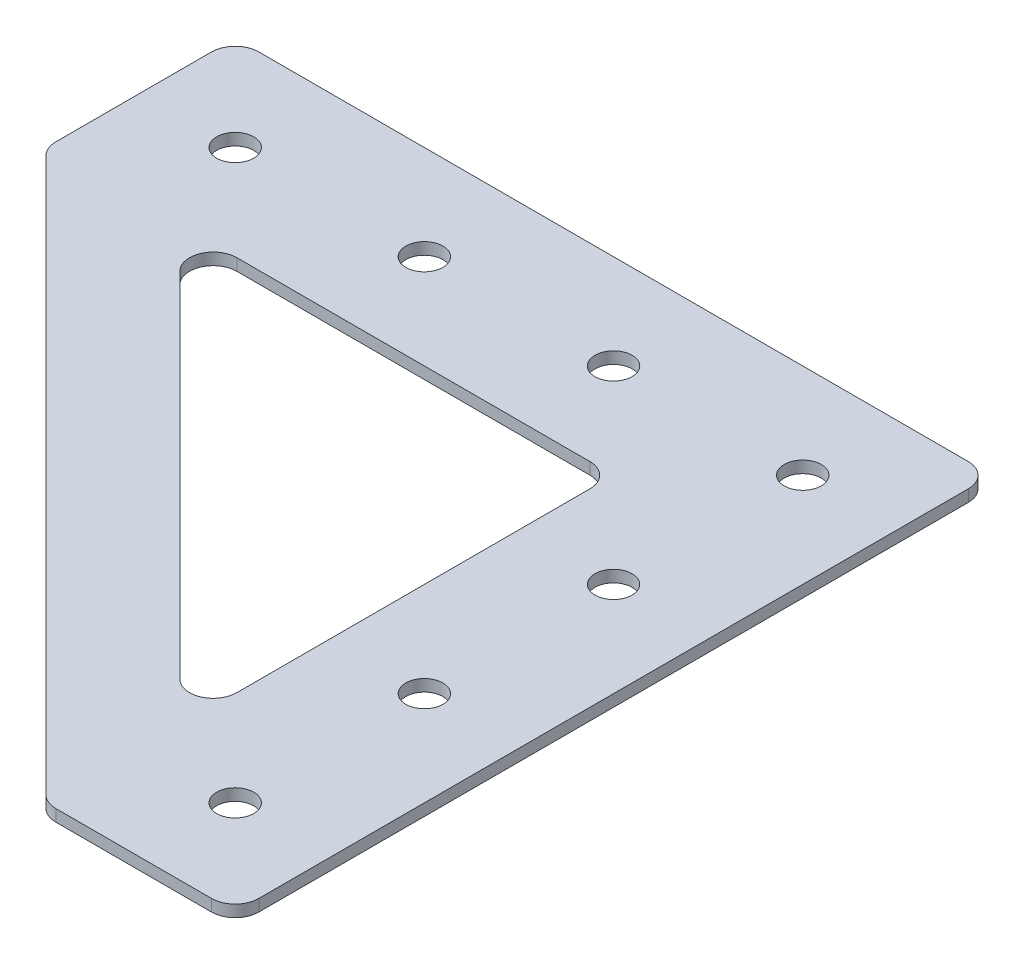
SolidWorks part; units mm, degrees
material "6061-T6 (SS)"
ref_plane "Front Plane" through (0, 0, 0) normal (0, 0, 1) x (1, 0, 0)
ref_plane "Top Plane" through (0, 0, 0) normal (0, 1, 0) x (1, 0, 0)
ref_plane "Right Plane" through (0, 0, 0) normal (1, 0, 0) x (0, 0, -1)
sketch "Sketch1" plane through (0, 0, 0) normal (0, 1, 0) x (1, 0, 0)
  line L0 (-25.4, -25.4) -> (-25.4, -83.6395)
  line L1 (0, 0) -> (-101.6, 0)
  line L2 (0, 0) -> (0, -101.6)
  line L3 (0, -101.6) -> (-25.4, -101.6)
  line L4 (-101.6, 0) -> (-101.6, -25.4)
  line L5 (-25.4, -25.4) -> (-83.6395, -25.4)
  line L6 (-25.4, -101.6) -> (-101.6, -25.4)
  line L7 (-25.4, -83.6395) -> (-83.6395, -25.4)
  line L8 (-25.4, -25.4) -> (-101.6, -25.4) construction
  line L9 (-25.4, -25.4) -> (-25.4, -101.6) construction
  dimension "D1" = 101.6
  dimension "D2" = 101.6
  dimension "D4" = 12.7
  dimension "D3" = 25.4
extrude "Boss-Extrude1" add sketch "Sketch1" along normal blind 1.5875
sketch "Sketch2" plane through (0, 1.5875, 0) normal (0, 1, 0) x (1, 0, 0)
  line L0 (0, 0) -> (-101.6, 0) construction
  line L1 (0, -101.6) -> (0, 0) construction
  circle A0 centre (-12.7, -12.7) radius 2.4892
  dimension "D3" = 4.9784
  dimension "D1" = 12.7
  dimension "D2" = 12.7
extrude "Cut-Extrude1" cut sketch "Sketch2" against normal through all
pattern_linear "LPattern1" count 4 spacing 25.4 along (0, 0, 1) count 4 spacing 25.4 along (-1, 0, 0) of "Cut-Extrude1"
fillet "Fillet1" radius 3.175 8 edges at (-25.4, 0.7937, 83.6395) (-25.4, 0.7937, 25.4) (-83.6395, 0.7937, 25.4) (0, 0.7937, 101.6) (-25.4, 0.7937, 101.6) (-101.6, 0.7937, 25.4) (0, 0.7937, 0) (-101.6, 0.7937, 0)
